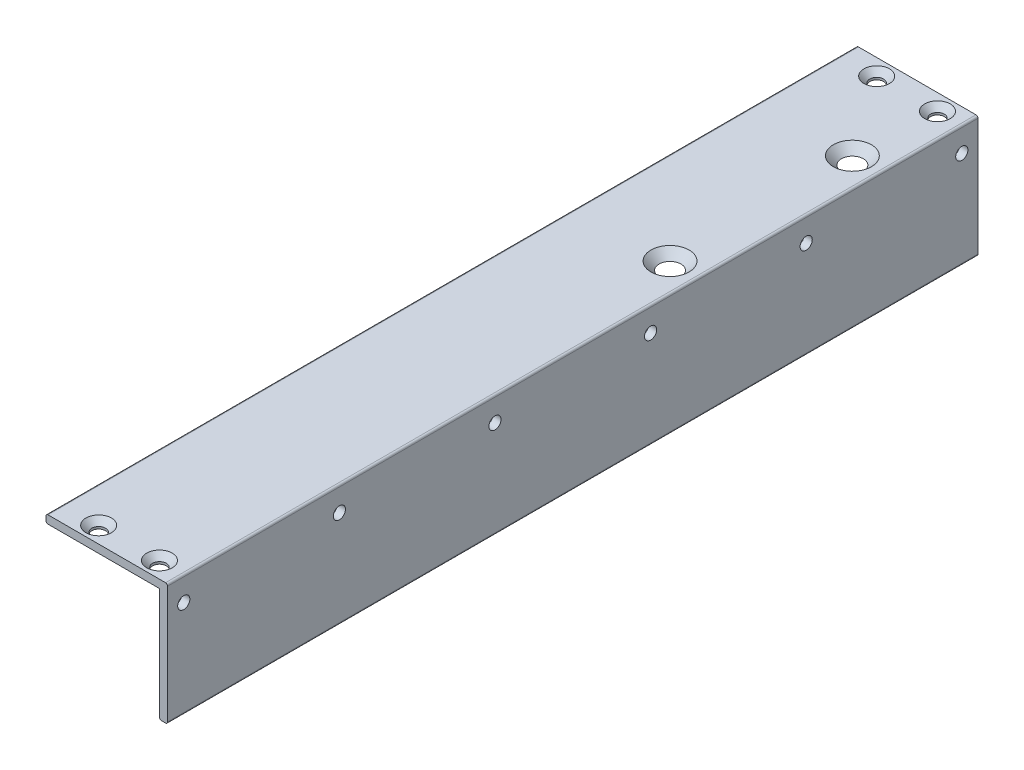
SolidWorks part; units mm, degrees
ref_plane "Front Plane" through (0, 0, 0) normal (0, 0, 1) x (1, 0, 0)
ref_plane "Top Plane" through (0, 0, 0) normal (0, 1, 0) x (1, 0, 0)
ref_plane "Right Plane" through (0, 0, 0) normal (1, 0, 0) x (0, 0, -1)
sketch "Sketch1" plane through (0, 0, 0) normal (0, 0, 1) x (1, 0, 0)
  line L0 (0, 0) -> (0, 28)
  line L1 (0, 28) -> (-28, 28)
  line L2 (-28, 28) -> (-28, 30)
  line L3 (-28, 30) -> (2, 30)
  line L4 (2, 30) -> (2, 0)
  line L5 (2, 0) -> (0, 0)
extrude "Extrude1" add sketch "Sketch1" along normal blind 200
fillet "Fillet1" radius 0.5 5 edges at (0, 0, 100) (2, 0, 100) (2, 30, 100) (-28, 30, 100) (-28, 28, 100)
sketch "Sketch2" plane through (0, 30, 0) normal (0, -1, 0) x (1, 0, 0)
  line L0 (1.5, 24) -> (-27.5, 24) construction
  line L1 (-27.5, 196) -> (1.5, 196) construction
  line L2 (-27.5, 200) -> (-27.5, 0) construction
  line L3 (-27.5, 69) -> (1.5, 69) construction
  line L4 (1.5, 200) -> (1.5, 0) construction
  line L5 (-27.5, 4) -> (1.5, 4) construction
  line L6 (-27.5, 0) -> (-27.5, 200) construction
  point P6 (-5, 24)
  point P9 (-5, 69)
  point P14 (-4, 4)
  point P15 (-19, 4)
  point P18 (-19, 196)
  point P19 (-4, 196)
hole_wizard "CSK for M4 Countersunk Flat Head Screw1" positions "3DSketch2" profile "Sketch4" countersink size "M4" standard "DIN" end condition up to next
sketch3d "3DSketch2"
  point P0 (-5, 30, 69)
  point P3 (-5, 30, 24)
sketch "Sketch4" plane through (-5, 30, 69) normal (1, 0, 0) x (0, 0, 1)
  line L0 (0, 0) -> (0, 2)
  line L1 (0, 2) -> (2.25, 2)
  line L2 (2.25, 2) -> (2.25, 2.45)
  line L3 (2.25, 2.45) -> (4.7, 0)
  line L5 (4.7, 0) -> (0, 0)
  line L6 (-2.25, 2.45) -> (-4.7, 0) construction
  line L11 (0, -6.35) -> (0, 107.95) construction
  dimension "Thru Hole Dia." = 4.5
  dimension "Thru Hole Depth" = 2
  dimension "Near C'Sink Dia." = 9.4
  dimension "Near C'Sink Angle" = 90
hole_wizard "CSK for M3 Countersunk Flat Head Screw1" positions "3DSketch3" profile "Sketch5" countersink size "M3" standard "DIN" end condition up to next
sketch3d "3DSketch3"
  point P0 (-19, 30, 4)
  point P3 (-4, 30, 4)
sketch "Sketch5" plane through (-19, 30, 4) normal (1, 0, 0) x (0, 0, 1)
  line L0 (0, 0) -> (0, 2)
  line L1 (0, 2) -> (1.7, 2)
  line L2 (1.7, 2) -> (1.7, 1.45)
  line L3 (1.7, 1.45) -> (3.15, 0)
  line L5 (3.15, 0) -> (0, 0)
  line L6 (-1.7, 1.45) -> (-3.15, 0) construction
  line L11 (0, -6.35) -> (0, 107.95) construction
  dimension "Thru Hole Dia." = 3.4
  dimension "Thru Hole Depth" = 2
  dimension "Near C'Sink Dia." = 6.3
  dimension "Near C'Sink Angle" = 90
hole_wizard "CSK for M3 Countersunk Flat Head Screw2" positions "3DSketch4" profile "Sketch6" countersink size "M3" standard "DIN" end condition up to next
sketch3d "3DSketch4"
  point P0 (-19, 30, 196)
  point P3 (-4, 30, 196)
sketch "Sketch6" plane through (-19, 30, 196) normal (1, 0, 0) x (0, 0, 1)
  line L0 (0, 0) -> (0, 2)
  line L1 (0, 2) -> (1.7, 2)
  line L2 (1.7, 2) -> (1.7, 1.45)
  line L3 (1.7, 1.45) -> (3.15, 0)
  line L5 (3.15, 0) -> (0, 0)
  line L6 (-1.7, 1.45) -> (-3.15, 0) construction
  line L11 (0, -6.35) -> (0, 107.95) construction
  dimension "Thru Hole Dia." = 3.4
  dimension "Thru Hole Depth" = 2
  dimension "Near C'Sink Dia." = 6.3
  dimension "Near C'Sink Angle" = 90
sketch "Sketch7" plane through (2, 0, 0) normal (1, 0, 0) x (0, 0, -1)
  line L0 (-4, 29.5) -> (-4, 0.5) construction
  line L1 (0, 29.5) -> (-200, 29.5) construction
  line L2 (-200, 0.5) -> (0, 0.5) construction
  point P6 (-4, 24)
hole_wizard "M3 Tapped Hole1" positions "3DSketch5" profile "Sketch9" tap size "M3" standard "DIN" end condition up to next
sketch3d "3DSketch5"
  point P0 (2, 24, 4)
sketch "Sketch9" plane through (2, 24, 4) normal (0, 1, 0) x (0, 0, -1)
  line L0 (0, 0) -> (0, 2.001)
  line L1 (0, 2.001) -> (1.5, 2.001)
  line L2 (1.5, 2.001) -> (1.5, 0)
  line L5 (1.5, 0) -> (0, 0)
  line L11 (0, -6.35) -> (0, 107.95) construction
  dimension "Thread Major Dia." = 3
  dimension "Thru Tap Drill Depth" = 2.001
pattern_linear "LPattern1" count 6 spacing 38.4 along (0, 0, 1) of "M3 Tapped Hole1"
